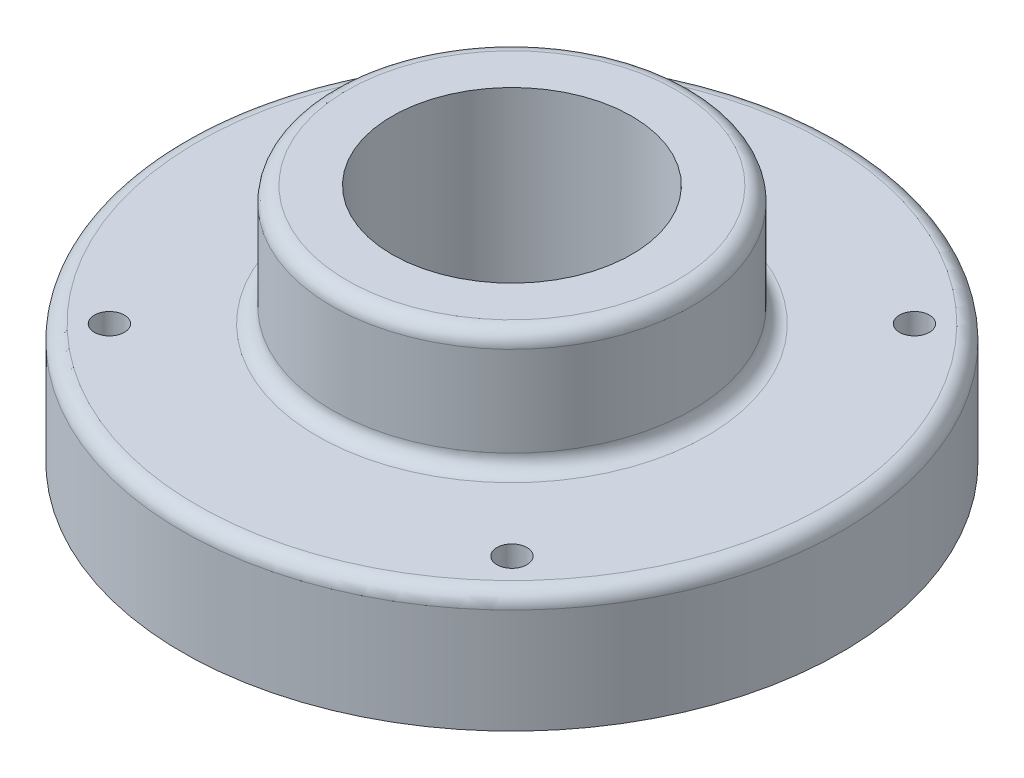
SolidWorks part; units mm, degrees
ref_plane "Front Plane" through (0, 0, 0) normal (0, 0, 1) x (1, 0, 0)
ref_plane "Top Plane" through (0, 0, 0) normal (0, 1, 0) x (1, 0, 0)
ref_plane "Right Plane" through (0, 0, 0) normal (1, 0, 0) x (0, 0, -1)
sketch "Sketch1" plane through (0, 0, 0) normal (0, 0, 1) x (1, 0, 0)
  line L0 (0, 0) -> (0, 25.4) construction
  line L1 (12.7, 25.4) -> (17.4625, 25.4)
  line L2 (19.05, 23.8125) -> (19.05, 14.2875)
  line L3 (20.6375, 12.7) -> (33.3375, 12.7)
  line L4 (34.925, 11.1125) -> (34.925, 0)
  line L5 (34.925, 0) -> (25.4, 0)
  line L6 (25.4, 0) -> (25.4, 3.175)
  line L7 (22.225, 6.35) -> (12.7, 6.35)
  line L8 (12.7, 6.35) -> (12.7, 25.4)
  arc A0 (33.3375, 12.7) -> (34.925, 11.1125) centre (33.3375, 11.1125) cw
  arc A1 (20.6375, 12.7) -> (19.05, 14.2875) centre (20.6375, 14.2875) cw
  arc A2 (17.4625, 25.4) -> (19.05, 23.8125) centre (17.4625, 23.8125) cw
  arc A3 (25.4, 3.175) -> (22.225, 6.35) centre (22.225, 3.175) ccw
  point P15 (34.925, 12.7)
  dimension "D8" = 1.5875
  dimension "D9" = 3.175
  dimension "D1" = 25.4
  dimension "D2" = 19.05
  dimension "D3" = 12.7
  dimension "D4" = 19.05
  dimension "D5" = 34.925
  dimension "D6" = 12.7
  dimension "D7" = 25.4
revolve "Revolve1" add sketch "Sketch1" angle 360 about L0
sketch "Sketch2" plane through (0, 12.7, 0) normal (0, 1, 0) x (1, 0, 0)
  line L0 (0, 0) -> (0, 30.1625) construction
  line L1 (-21.3281, 21.3281) -> (0, 0) construction
  circle A0 centre (0, 0) radius 30.1625 construction
  circle A2 centre (-21.3281, 21.3281) radius 1.5875
  circle A3 centre (21.3281, 21.3281) radius 1.5875
  circle A4 centre (21.3281, -21.3281) radius 1.5875
  circle A5 centre (-21.3281, -21.3281) radius 1.5875
  point P15 (0, 0)
  dimension "D1" = 60.325
  dimension "D2" = 3.175
  dimension "D3" = 45
  dimension "D4" = 4
extrude "Cut-Extrude1" cut sketch "Sketch2" against normal through all
sketch "Sketch3" plane through (0, 12.7, 0) normal (0, 1, 0) x (1, 0, 0)
  point P0 (-21.3281, 21.3281)
  point P5 (21.3281, 21.3281)
  point P6 (21.3281, -21.3281)
  point P7 (-21.3281, -21.3281)
  point P8 (0, 0)
  dimension "D1" = 4
